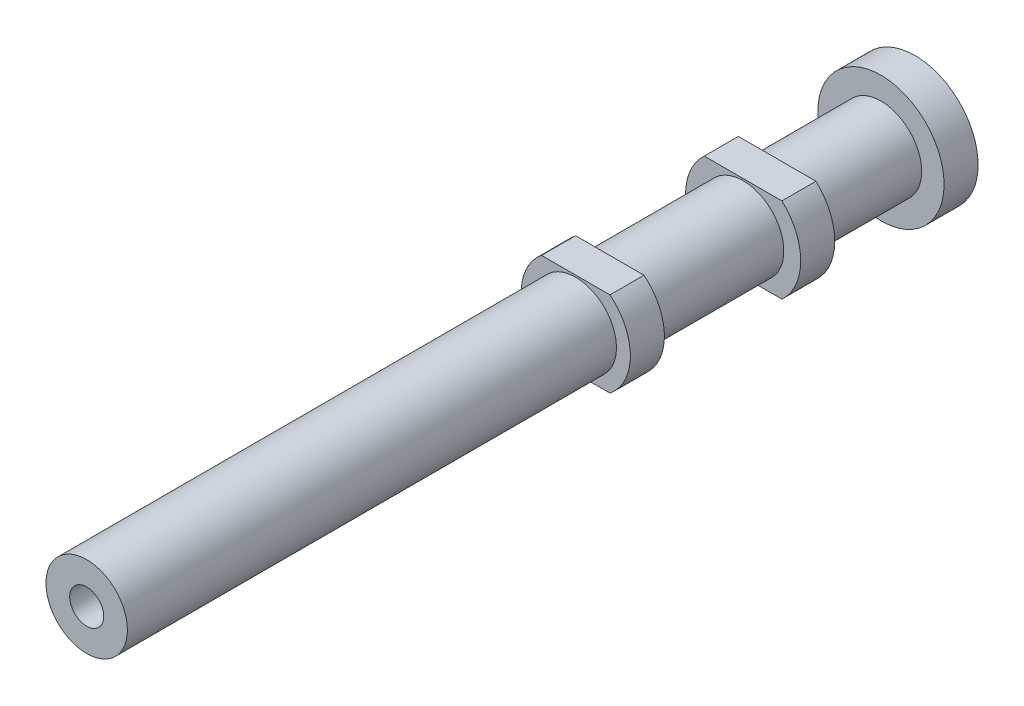
SolidWorks part; units mm, degrees
material "IS513 CR2"
ref_plane "Front" through (0, 0, 0) normal (0, 0, 1) x (1, 0, 0)
ref_plane "Top" through (0, 0, 0) normal (0, 1, 0) x (1, 0, 0)
ref_plane "Right" through (0, 0, 0) normal (1, 0, 0) x (0, 0, -1)
sketch "Sketch1" plane through (0, 0, 0) normal (0, 0, 1) x (1, 0, 0)
  circle A0 centre (0, 0) radius 1.435
  dimension "D1" = 2.87
extrude "Boss-Extrude1" add sketch "Sketch1" along normal mid plane 29.2
sketch "Sketch2" plane through (0, 0, 14.6) normal (0, 0, 1) x (1, 0, 0)
  circle A0 centre (0, 0) radius 0.6
  dimension "D1" = 1.2
extrude "Cut-Extrude1" cut sketch "Sketch2" against normal blind 5
sketch "Sketch3" plane through (0, 0, 0) normal (0, 1, 0) x (1, 0, 0)
  line L0 (-1.435, -14.6) -> (1.435, -14.6) construction
  line L1 (1.435, 3.84) -> (1.925, 3.84)
  line L3 (1.435, 2.64) -> (1.925, 2.64)
  line L4 (1.925, 3.84) -> (1.925, 2.64)
  line L5 (1.435, 9.74) -> (2.03, 9.74)
  line L7 (1.435, 8.54) -> (2.03, 8.54)
  line L8 (2.03, 9.74) -> (2.03, 8.54)
  line L9 (0, 14.6) -> (0, 12.6405) construction
  line L10 (1.435, 14.6) -> (2.225, 14.6)
  line L11 (1.435, 14.6) -> (1.435, 13.4)
  line L12 (1.435, 13.4) -> (2.225, 13.4)
  line L13 (2.225, 14.6) -> (2.225, 13.4)
  line L14 (1.435, 14.6) -> (-1.435, 14.6) construction
  line L15 (1.435, 9.74) -> (1.435, 8.54)
  line L16 (1.435, 3.84) -> (1.435, 2.64)
  line L17 (1.435, -14.6) -> (1.435, 14.6) construction
  dimension "D1" = 18.44
  dimension "D2" = 24.34
  dimension "D3" = 4.45
  dimension "D4" = 1.2
  dimension "D5" = 4.06
  dimension "D6" = 3.85
  dimension "D7" = 1.2
  dimension "D8" = 1.2
revolve "Revolve1" add sketch "Sketch3" angle 360 about L9
sketch "Sketch4" plane through (0, 0, 14.6) normal (0, 0, 1) x (1, 0, 0)
  line L0 (0, 0) -> (4.1277, 0) construction
  line L1 (-2, 2.5) -> (2, 2.5)
  line L2 (-2, 2.5) -> (-2, 1.5)
  line L3 (-2, 1.5) -> (2, 1.5)
  line L4 (2, 2.5) -> (2, 1.5)
  line L5 (2, -2.5) -> (2, -1.5)
  line L6 (-2, -1.5) -> (2, -1.5)
  line L7 (-2, -2.5) -> (-2, -1.5)
  line L8 (-2, -2.5) -> (2, -2.5)
  line L9 (0, 0) -> (0, 1.5) construction
  dimension "D1" = 4
  dimension "D2" = 1
  dimension "D3" = 3
extrude "Cut-Extrude2" cut sketch "Sketch4" against normal up to surface (24.34 mm away) up to face at (1.435, 0, -9.74)
